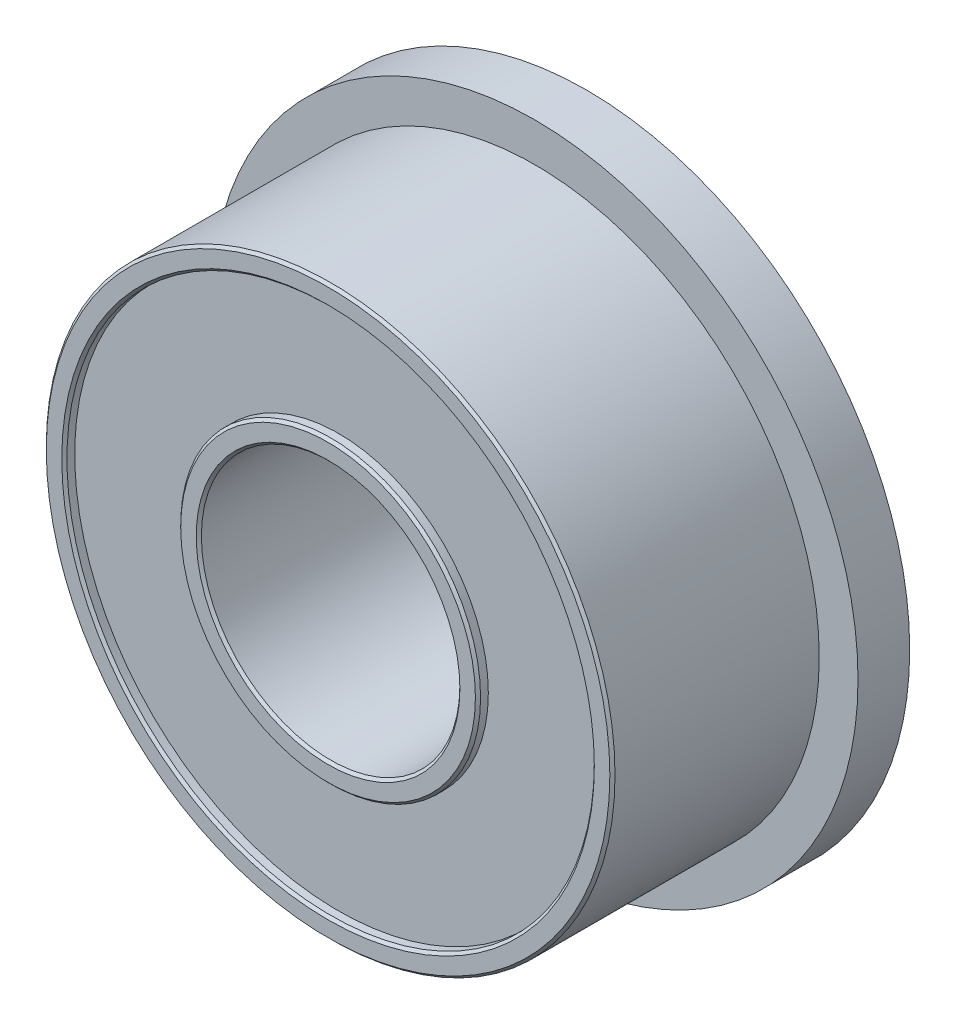
SolidWorks part; units mm, degrees
material "普通碳钢"
ref_plane "前视基准面" through (0, 0, 0) normal (0, 0, 1) x (1, 0, 0)
ref_plane "上视基准面" through (0, 0, 0) normal (0, 1, 0) x (1, 0, 0)
ref_plane "右视基准面" through (0, 0, 0) normal (1, 0, 0) x (0, 0, -1)
sketch "草图1" plane through (0, 0, 0) normal (0, 0, 1) x (1, 0, 0)
  circle A0 centre (0, 0) radius 2.5
  circle A1 centre (0, 0) radius 5.5
  dimension "D1" = 5
extrude "凸台-拉伸1" add sketch "草图1" along normal mid plane 5
sketch "草图3" plane through (0, 0, -2.5) normal (0, 0, -1) x (-1, 0, 0)
  circle A0 centre (0, 0) radius 2.5 construction
  circle A1 centre (0, 0) radius 2.5
  circle A2 centre (0, 0) radius 6.25
extrude "凸台-拉伸2" add sketch "草图3" against normal blind 1
sketch "草图4" plane through (0, 0, 2.5) normal (0, 0, 1) x (1, 0, 0)
  circle A2 centre (0, 0) radius 2.9
  circle A3 centre (0, 0) radius 2.9
  circle A6 centre (0, 0) radius 5.1
  circle A7 centre (0, 0) radius 5.1
  dimension "D1" = 0.4
  dimension "D2" = 0.4
extrude "切除-拉伸1" cut sketch "草图4" against normal blind 0.2
mirror "镜向1" about plane through (0, 0, 0) normal (0, 0, 1) of "切除-拉伸1"
chamfer "倒角1" distance 0.05 angle 45 7 edges at (2.5, 0, -2.5) (2.9, 0, -2.5) (2.9, 0, 2.5) (2.5, 0, 2.5) (5.5, 0, 2.5) (5.1, 0, 2.5) (5.1, 0, -2.5)
move or copy body "实体-移动/复制3" [suppressed] bodies to move or copy 109
move or copy body "实体-移动/复制1" [suppressed] bodies to move or copy 109
move or copy body "实体-移动/复制2" [suppressed] bodies to move or copy 109
equation "\"内径\"= 2"
equation "\"外径\"= 5"
equation "\"法兰外径\"= 6.1"
equation "\"宽度\"= 2.3"
equation "\"法兰宽度\"= 0.6"
equation "\"D1@草图1\"=\"内径\""
equation "\"D2@草图1\"=\"外径\""
equation "\"D1@草图3\"=\"法兰外径\""
equation "\"D1@凸台-拉伸1\"=\"宽度\""
equation "\"D1@凸台-拉伸2\"=\"法兰宽度\""
